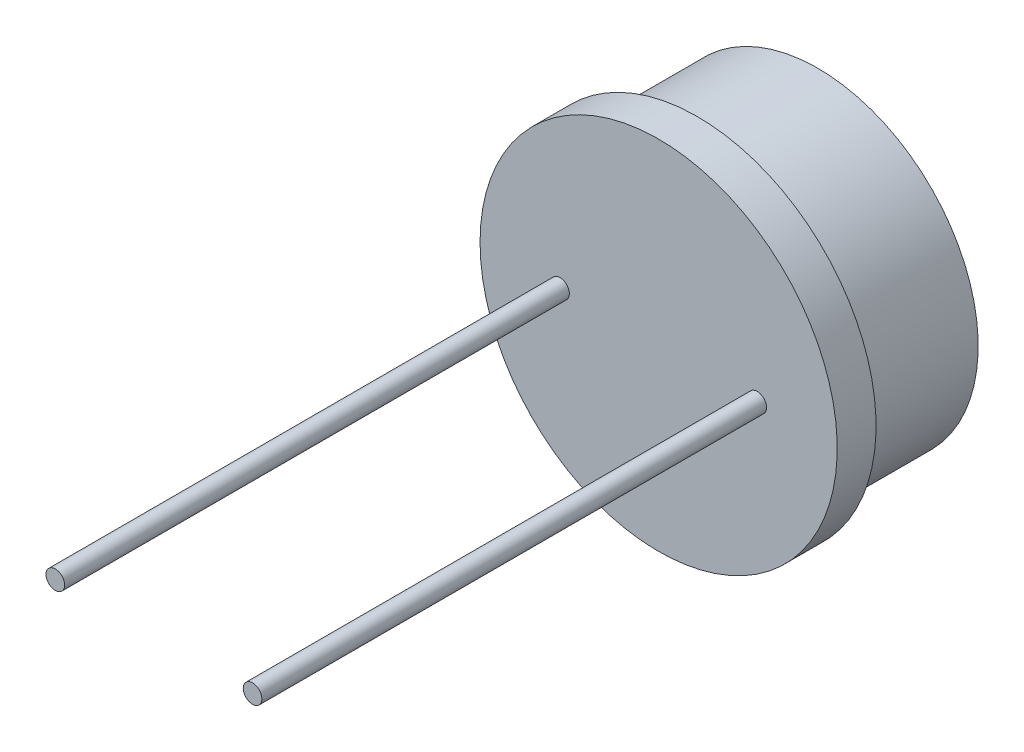
SolidWorks part; units mm, degrees
ref_plane "Front Plane" through (0, 0, 0) normal (0, 0, 1) x (1, 0, 0)
ref_plane "Top Plane" through (0, 0, 0) normal (0, 1, 0) x (1, 0, 0)
ref_plane "Right Plane" through (0, 0, 0) normal (1, 0, 0) x (0, 0, -1)
sketch "Sketch1" plane through (0, 0, 0) normal (0, 1, 0) x (1, 0, 0)
  line L0 (0, 0) -> (4.6, 0)
  line L1 (4.6, 0) -> (4.6, 1)
  line L2 (4.6, 1) -> (4.13, 1)
  line L3 (4.13, 1) -> (4.13, 4.1)
  line L4 (4.13, 4.1) -> (3.63, 4.1)
  line L5 (3.63, 4.1) -> (3.63, 3.9)
  line L6 (3.63, 3.9) -> (0, 3.9)
  line L7 (0, 3.9) -> (0, 0)
  point P3 (3.88, 4.1)
  dimension "D1" = 4.6
  dimension "D2" = 0.2
  dimension "D3" = 4.1
  dimension "D4" = 4.13
  dimension "D5" = 0.5
  dimension "D6" = 1
revolve "Revolve1" add sketch "Sketch1" angle 360 about L7
sketch "Sketch2" plane through (0, 0, 0) normal (0, 0, 1) x (1, 0, 0)
  line L0 (-2.54, 0) -> (2.54, 0) construction
  circle A0 centre (-2.54, 0) radius 0.24
  circle A1 centre (2.54, 0) radius 0.24
  dimension "D1" = 0.48
  dimension "D2" = 5.08
extrude "Boss-Extrude1" add sketch "Sketch2" along normal blind 13
